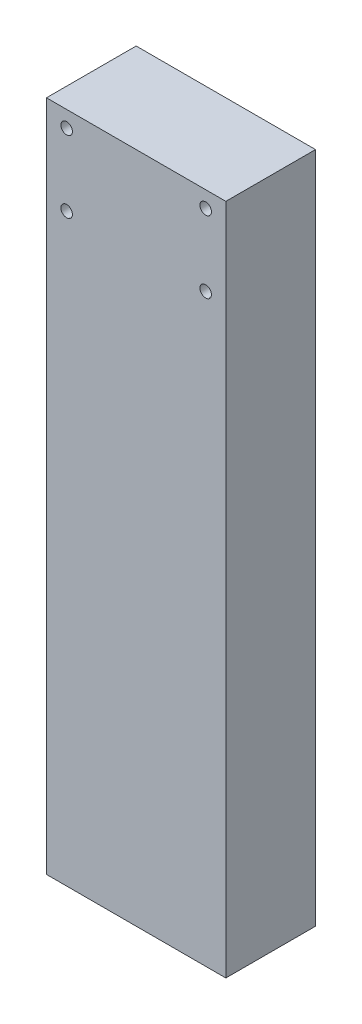
SolidWorks part; units mm, degrees
material "Oak"
ref_plane "Front Plane" through (0, 0, 0) normal (0, 0, 1) x (1, 0, 0)
ref_plane "Top Plane" through (0, 0, 0) normal (0, 1, 0) x (1, 0, 0)
ref_plane "Right Plane" through (0, 0, 0) normal (1, 0, 0) x (0, 0, -1)
sketch "Sketch1" plane through (0, 0, 0) normal (0, 1, 0) x (1, 0, 0)
  line L1 (-50.8, -25.4) -> (50.8, -25.4)
  line L2 (-50.8, -25.4) -> (-50.8, 25.4)
  line L3 (-50.8, 25.4) -> (50.8, 25.4)
  line L4 (50.8, -25.4) -> (50.8, 25.4)
  line L5 (-50.8, -25.4) -> (50.8, 25.4) construction
  line L6 (-50.8, 25.4) -> (50.8, -25.4) construction
  point P0 (0, 0)
  dimension "D1" = 101.6
  dimension "D2" = 50.8
extrude "Boss-Extrude1" add sketch "Sketch1" along normal blind 381
hole_wizard "1/4 Clearance Hole2" positions "Sketch4" profile "Sketch5" hole size "1/4" standard "ANSI Inch" end condition through all
sketch "Sketch4" plane through (0, 128.0439, 25.4) normal (0, 0, 1) x (1, 0, 0)
  point P0 (39.37, 243.7168)
  point P1 (39.37, 203.0768)
  point P2 (-39.37, 203.0768)
  point P3 (-39.37, 243.7168)
sketch "Sketch5" plane through (39.37, 371.7608, 25.4) normal (1, 0, 0) x (0, -1, 0)
  line L0 (0, 0) -> (0, 50.8)
  line L1 (0, 50.8) -> (3.2639, 50.8)
  line L2 (3.2639, 50.8) -> (3.2639, 0)
  line L3 (3.2639, 0) -> (0, 0)
  line L4 (0, -6.35) -> (0, 107.95) construction
  dimension "Thru Hole Dia." = 6.5278
  dimension "Thru Hole Depth" = 50.8
